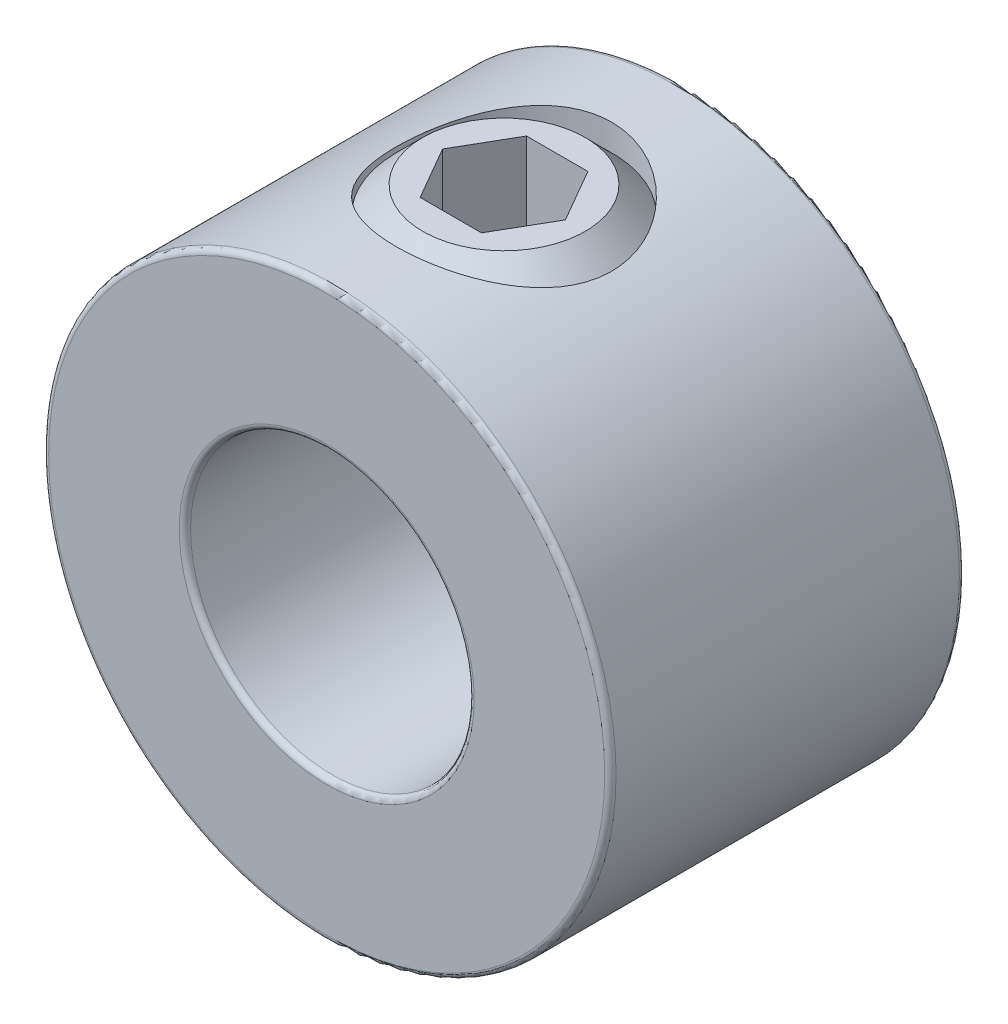
SolidWorks part; units mm, degrees
ref_plane "Front Plane" through (0, 0, 0) normal (0, 0, 1) x (1, 0, 0)
ref_plane "Top Plane" through (0, 0, 0) normal (0, 1, 0) x (1, 0, 0)
ref_plane "Right Plane" through (0, 0, 0) normal (1, 0, 0) x (0, 0, -1)
sketch "Sketch1" plane through (0, 0, 0) normal (0, 0, 1) x (1, 0, 0)
  circle A0 centre (0, 0) radius 6.35
  circle A1 centre (0, 0) radius 3.175
  point P4 (6.35, 0)
  dimension "Bore Dia" = 6.35
  dimension "OD" = 12.7
extrude "Extrude1" add sketch "Sketch1" along normal mid plane 7.9375
sketch "Sketch2" plane through (41.275, 0, 0) normal (0, -1, 0) x (0, 0, -1)
  line L0 (3.9688, -41.275) -> (-3.9688, -41.275) construction
  line L1 (-3.9688, -34.925) -> (-3.9688, -47.625) construction
  line L2 (3.9688, -47.625) -> (3.9688, -34.925) construction
  circle A0 centre (0, -41.275) radius 2.413
  point P7 (0, -43.688)
  dimension "Set Screw Dia" = 4.826
extrude "Cut-Extrude1" cut sketch "Sketch2" against normal through all
fillet "Fillet1" radius 0.127 4 edges at (3.175, 0, -3.9688) (3.175, 0, 3.9688) (6.35, 0, -3.9688) (6.35, 0, 3.9688)
sketch "Sketch3" plane through (0, 0, 0) normal (0, 0, 1) x (1, 0, 0)
  line L0 (-1.8198, 3.175) -> (-0.7119, 3.175)
  line L1 (0, 3.8869) -> (-0.7119, 3.175)
  line L2 (0, 3.8869) -> (0, 6.35)
  line L3 (0, 6.35) -> (-1.8198, 6.35)
  line L4 (-2.413, 3.7682) -> (-2.413, 5.7568)
  line L5 (0, 3.175) -> (0, 0) construction
  line L6 (-2.413, 3.7682) -> (-2.413, 3.175) construction
  line L7 (-2.413, 3.175) -> (-1.8198, 3.175) construction
  line L8 (-2.413, 5.7568) -> (-2.413, 6.35) construction
  line L9 (-1.8198, 3.175) -> (-2.413, 3.7682)
  line L10 (-2.413, 5.7568) -> (-1.8198, 6.35)
  line L11 (-2.413, 6.35) -> (-1.8198, 6.35) construction
  line L12 (-0.7119, 3.175) -> (0, 3.175) construction
  line L13 (0, 3.175) -> (0, 3.8869) construction
  circle A1 centre (0, 0) radius 3.175 construction
  dimension "Screw Length" = 3.175
  dimension "D2" = 0.5932
  dimension "D1" = 0.7119
revolve "Revolve1" add sketch "Sketch3" angle 360 about L5
sketch "Sketch4" plane through (3.3734, 6.35, 0) normal (0, -1, 0) x (0, 0, -1)
  line L1 (0, -1.9986) -> (-1.1906, -2.686)
  line L2 (-1.1906, -2.686) -> (-1.1906, -4.0608)
  line L3 (-1.1906, -4.0608) -> (0, -4.7483)
  line L4 (0, -4.7483) -> (1.1906, -4.0608)
  line L5 (1.1906, -4.0608) -> (1.1906, -2.686)
  line L6 (1.1906, -2.686) -> (0, -1.9986)
  circle A0 centre (0, -3.3734) radius 1.1906 construction
  circle A1 centre (0, -3.3734) radius 1.3748 construction
  dimension "D1" = 2.7496
  dimension "Hex Size" = 2.3813
extrude "Cut-Extrude2" cut sketch "Sketch4" along normal blind 2.3813
equation "\"D1@Fillet1\" = \"OD@Sketch1\"*.01"
equation "\"D1@Cut-Extrude2\" = \"Hex Size@Sketch4\""
equation "\"D2@Sketch3\" =(\"Set Screw Dia@Sketch2\"-\"D1@Sketch4\")/3.5"
equation "\"D1@Sketch3\" = \"D2@Sketch3\"*1.2"
